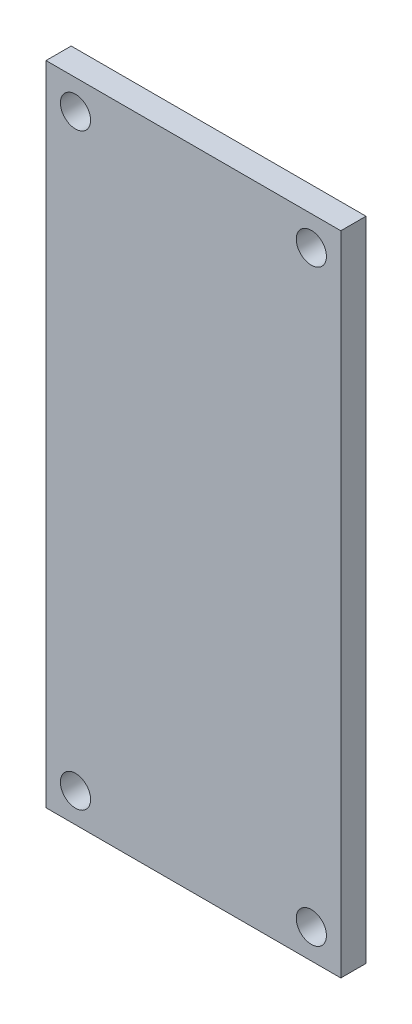
SolidWorks part; units mm, degrees
ref_plane "Front Plane" through (0, 0, 0) normal (0, 0, 1) x (1, 0, 0)
ref_plane "Top Plane" through (0, 0, 0) normal (0, 1, 0) x (1, 0, 0)
ref_plane "Right Plane" through (0, 0, 0) normal (1, 0, 0) x (0, 0, -1)
sketch "Sketch1" plane through (0, 0, 0) normal (0, 0, 1) x (1, 0, 0)
  line L0 (10.25, 0) -> (-10.25, 0) construction
  line L1 (-10.25, 22.5) -> (10.25, 22.5)
  line L2 (-10.25, 22.5) -> (-10.25, -22.5)
  line L3 (-10.25, -22.5) -> (10.25, -22.5)
  line L4 (10.25, 22.5) -> (10.25, -22.5)
  dimension "D1" = 20.5
  dimension "D2" = 45
extrude "Extrude1" add sketch "Sketch1" along normal blind 1.75
sketch "Sketch2" plane through (0, 0, 1.75) normal (0, 0, 1) x (1, 0, 0)
  line L0 (-10.25, -22.5) -> (10.25, -22.5) construction
  line L1 (-10.25, 22.5) -> (-10.25, -22.5) construction
  line L2 (10.25, 22.5) -> (-10.25, 22.5) construction
  line L3 (10.25, -22.5) -> (10.25, 22.5) construction
  circle A0 centre (8.2, -20.45) radius 1.05
  circle A1 centre (-8.2, 20.45) radius 1.05
  circle A2 centre (-8.2, -20.45) radius 1.05
  circle A3 centre (8.2, 20.45) radius 1.05
  dimension "D1" = 2.1
  dimension "D2" = 2.05
  dimension "D3" = 2.05
  dimension "D4" = 2.1
  dimension "D5" = 1
  dimension "D6" = 2.05
  dimension "D7" = 2.05
  dimension "D8" = 2.05
  dimension "D9" = 2.05
  dimension "D10" = 2.05
extrude "Cut-Extrude1" cut sketch "Sketch2" against normal up to surface (1.75 mm away) up to face at (0, 0, 0)
